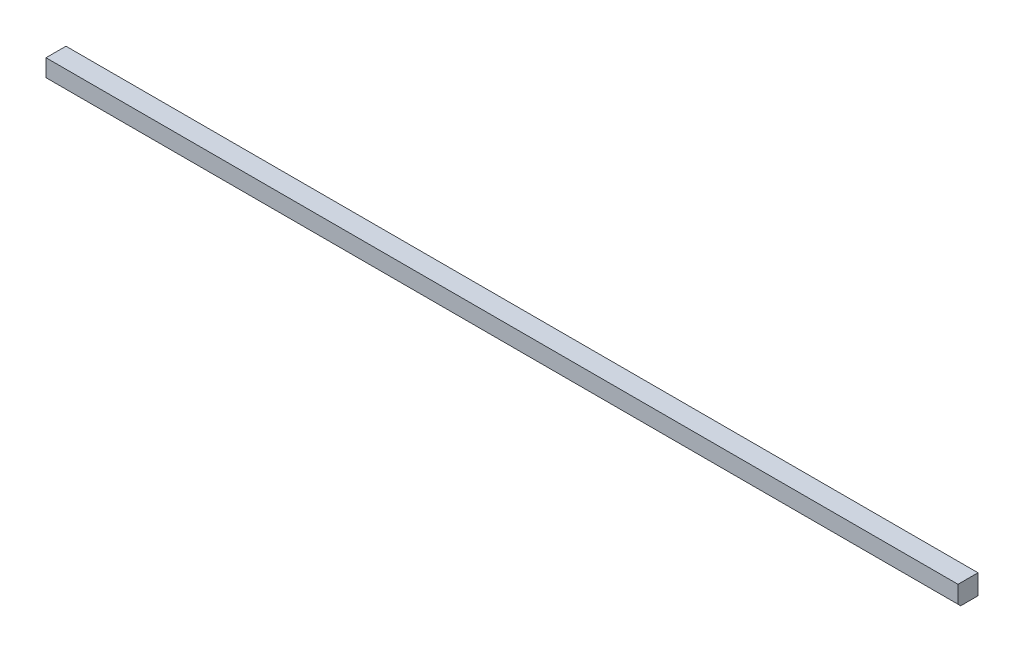
SolidWorks part; units mm, degrees
material "Oak"
ref_plane "Front Plane" through (0, 0, 0) normal (0, 0, 1) x (1, 0, 0)
ref_plane "Top Plane" through (0, 0, 0) normal (0, 1, 0) x (1, 0, 0)
ref_plane "Right Plane" through (0, 0, 0) normal (1, 0, 0) x (0, 0, -1)
sketch "Sketch1" plane through (0, 0, 0) normal (0, 1, 0) x (1, 0, 0)
  line L1 (0, 0) -> (869.95, 0)
  line L2 (0, 0) -> (0, 19.05)
  line L3 (0, 19.05) -> (869.95, 19.05)
  line L4 (869.95, 0) -> (869.95, 19.05)
  dimension "D1" = 19.05
  dimension "D2" = 869.95
extrude "Boss-Extrude1" add sketch "Sketch1" along normal blind 19.05
chamfer "Chamfer1" distance 2.54 angle 45 1 edges at (434.975, 0, 0)
